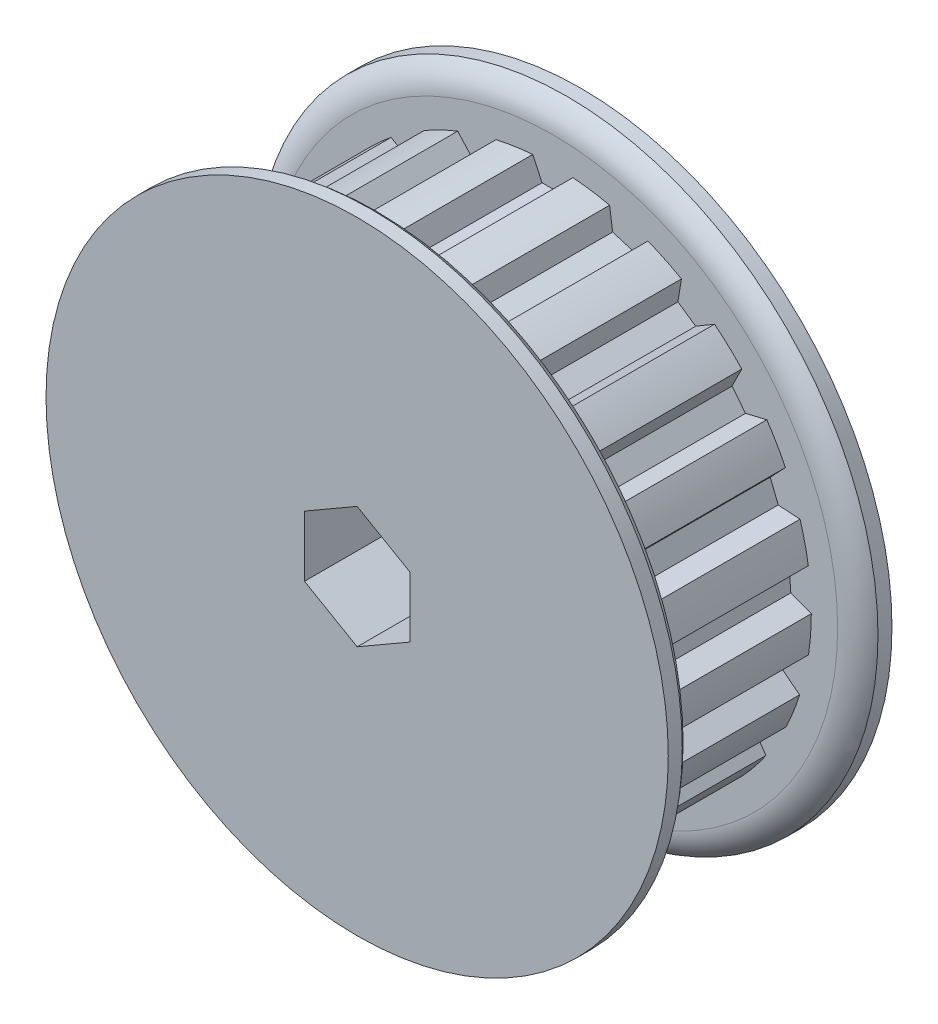
SolidWorks part; units mm, degrees
ref_plane "Front Plane" through (0, 0, 0) normal (0, 0, 1) x (1, 0, 0)
ref_plane "Top Plane" through (0, 0, 0) normal (0, 1, 0) x (1, 0, 0)
ref_plane "Right Plane" through (0, 0, 0) normal (1, 0, 0) x (0, 0, -1)
sketch "Sketch1" plane through (0, 0, 0) normal (0, 0, 1) x (1, 0, 0)
  line L0 (-1.2827, 16.4719) -> (-0.6905, 15.2019)
  line L1 (-0.6905, 15.2019) -> (0.6905, 15.2019)
  line L2 (0.6905, 15.2019) -> (1.2827, 16.4719)
  line L3 (-1.2827, 16.4719) -> (1.2827, 16.4719)
  line L4 (0, 0) -> (0, 15.2019) construction
  line L5 (0, 15.2019) -> (0, 17.4879) construction
  circle A0 centre (0, 0) radius 16.9799 construction
  circle A1 centre (0, 0) radius 19.8882 construction
  circle A2 centre (0, 0) radius 16.5218 construction
  point P6 (0, 16.4719)
  point P11 (0, 16.9799)
  point P13 (0, 19.8882)
  point P14 (0, 16.5218)
  dimension "D1" = 1.016
  dimension "D2" = 0.508
sketch "Sketch2" plane through (0, 0, 0) normal (1, 0, 0) x (0, 0, -1)
  line L0 (-11.1125, 3.175) -> (11.1125, 3.175)
  line L1 (-11.1125, 3.175) -> (-11.1125, 11.9126)
  line L2 (-11.1125, 11.9126) -> (-3.1877, 11.9126)
  line L3 (-3.1877, 11.9126) -> (-3.1877, 19.8882)
  line L4 (-3.1877, 19.8882) -> (-1.397, 19.8882) construction
  line L5 (-1.397, 19.8882) -> (-1.397, 16.5218) construction
  line L6 (-1.397, 16.5218) -> (9.3218, 16.5218)
  line L7 (9.3218, 16.5218) -> (9.3218, 19.8882) construction
  line L8 (9.3218, 19.8882) -> (11.1125, 19.8882) construction
  line L9 (11.1125, 19.8882) -> (11.1125, 3.175)
  line L10 (-11.1125, 0) -> (11.1125, 0) construction
  line L13 (-3.1877, 19.8882) -> (-2.2923, 19.8882)
  line L14 (-1.397, 18.205) -> (-1.397, 16.5218)
  line L15 (9.3218, 16.5218) -> (9.3218, 18.205)
  line L16 (10.2172, 19.8882) -> (11.1125, 19.8882)
  arc A0 (-1.397, 18.205) -> (-2.2923, 19.8882) centre (-3.4269, 18.205) ccw
  arc A1 (9.3218, 18.205) -> (10.2172, 19.8882) centre (11.3517, 18.205) cw
  point P12 (-1.397, 18.205)
  point P14 (-2.2923, 19.8882)
  point P20 (9.3218, 18.205)
  point P21 (10.2172, 19.8882)
  point P25 (9.3218, 0)
  point P26 (-1.397, 0)
  dimension "Bore" = 6.35
  dimension "Hub Dia" = 23.8252
  dimension "Outside Width" = 14.3002
  dimension "Inside Width" = 10.7188
revolve "Revolve1" add sketch "Sketch2" angle 360 mid plane about L10
sketch "Sketch3" plane through (0, 0, 0) normal (0, 0, 1) x (1, 0, 0)
  line L0 (-0.6905, 15.2019) -> (0.6905, 15.2019) construction
  line L1 (0.6905, 15.2019) -> (1.2827, 16.4719) construction
  line L2 (-1.2827, 16.4719) -> (-0.6905, 15.2019) construction
  line L3 (-0.6905, 15.2019) -> (0.6905, 15.2019)
  line L4 (0.6905, 15.2019) -> (1.2827, 16.4719)
  line L5 (-1.2827, 16.4719) -> (-0.6905, 15.2019)
  circle A0 centre (0, 0) radius 16.5218 construction
  arc A1 (1.2827, 16.4719) -> (-1.2827, 16.4719) centre (0, 0) ccw
extrude "Cut-Extrude1" cut sketch "Sketch3" against normal up to vertex (9.3218 mm away) from vertex at 1.397 starting at point (0, 16.5218, 1.397)
pattern_circular "CirPattern1" count 21 over 360 about axis through (0, 0, 0) along (0, 0, 1) of "Cut-Extrude1"
sketch "Sketch4" plane through (0, 0, 0) normal (0, 1, 0) x (1, 0, 0)
  line L0 (0, -3.1877) -> (0, -11.1125) construction
  line L1 (-11.9126, -3.1877) -> (11.9126, -3.1877) construction
  line L2 (-11.9126, -11.1125) -> (11.9126, -11.1125) construction
  circle A0 centre (0, -7.1501) radius 1.5875
  dimension "D1" = 3.175
extrude "Cut-Extrude2" cut sketch "Sketch4" along normal through all
ref_plane "Plane1" through (0, 0, 7.1501) normal (0, 0, 1) x (1, 0, 0)
sketch "Sketch5" plane through (0, 0, 7.1501) normal (0, 0, 1) x (1, 0, 0)
  line L0 (0, 0) -> (0, 11.9126) construction
  line L1 (1.0795, 11.8063) -> (1.5875, 11.2983)
  line L2 (0, 11.8063) -> (1.0795, 11.8063)
  line L3 (0, 11.8063) -> (0, 3.175)
  line L4 (0, 3.175) -> (0.9525, 3.175)
  line L5 (1.5875, 11.2983) -> (1.5875, 3.81)
  line L6 (0.9525, 3.175) -> (1.5875, 3.81)
  circle A0 centre (0, 0) radius 11.9126 construction
  circle A1 centre (0, 0) radius 3.175 construction
  point P7 (1.5875, 3.175)
  point P9 (1.5875, 11.8063)
revolve "Revolve2" add sketch "Sketch5" angle 360 mid plane about L0
sketch "Sketch6" plane through (0, 11.8063, 0) normal (0, 1, 0) x (1, 0, 0)
  line L1 (0, -6.2336) -> (-0.7938, -6.6918)
  line L2 (-0.7938, -6.6918) -> (-0.7937, -7.6084)
  line L3 (-0.7937, -7.6084) -> (0, -8.0666)
  line L4 (0, -8.0666) -> (0.7938, -7.6084)
  line L5 (0.7938, -7.6084) -> (0.7938, -6.6918)
  line L6 (0.7938, -6.6918) -> (0, -6.2336)
  circle A0 centre (0, -7.1501) radius 0.7938 construction
  dimension "D1" = 1.5875
extrude "Cut-Extrude3" cut sketch "Sketch6" against normal blind 1.1906
pattern_circular "CirPattern2" count 2 every 90 about axis through (0, 0, 0) along (0, 0, 1) of "Cut-Extrude2", "Revolve2", "Cut-Extrude3"
sketch "Sketch7" plane through (0, 0, 11.1125) normal (0, 0, 1) x (1, 0, 0)
  line L1 (0, 3.8861) -> (-3.3655, 1.9431)
  line L2 (-3.3655, 1.9431) -> (-3.3655, -1.9431)
  line L3 (-3.3655, -1.9431) -> (0, -3.8861)
  line L4 (0, -3.8861) -> (3.3655, -1.9431)
  line L5 (3.3655, -1.9431) -> (3.3655, 1.9431)
  line L6 (3.3655, 1.9431) -> (0, 3.8861)
  circle A0 centre (0, 0) radius 3.3655 construction
  dimension "D1" = 6.731
extrude "Cut-Extrude4" cut sketch "Sketch7" against normal blind 50.8
sketch "Sketch8" plane through (0, 0, 3.1877) normal (0, 0, 1) x (1, 0, 0)
  circle A0 centre (0, 0) radius 12.7
  dimension "D1" = 25.4
extrude "Cut-Extrude5" cut sketch "Sketch8" along normal blind 50.8
equation "\"D2@Sketch1\" = \"D1@Sketch1\"/2"
equation "\"D1@Sketch4\" = \"Bore@Sketch2\"/2"
equation "\"D1@Sketch6\" = \"D1@Sketch4\"/2"
equation "\"D1@Cut-Extrude3\" = \"D1@Sketch6\"*.75"
